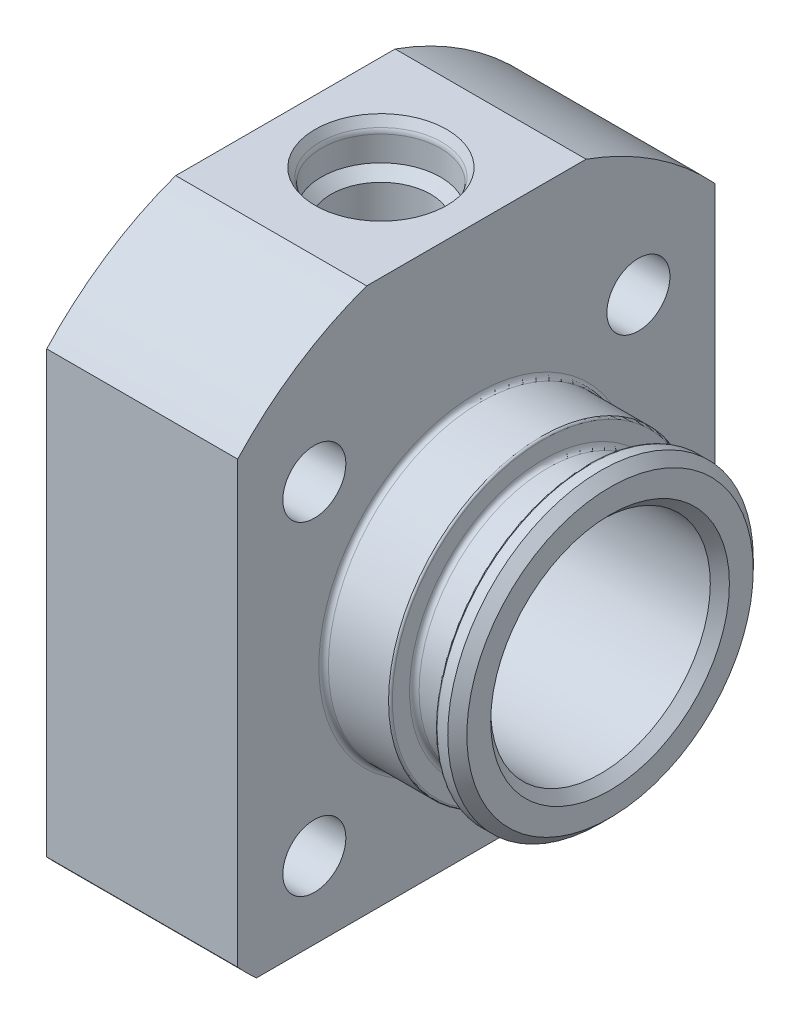
SolidWorks part; units mm, degrees
material "Сплав 3М ОСТ 1.92077-91"
ref_plane "Plane1" through (0, 0, 0) normal (0, 0, 1) x (1, 0, 0)
ref_plane "Plane2" through (0, 0, 0) normal (0, 1, 0) x (1, 0, 0)
ref_plane "Plane3" through (0, 0, 0) normal (1, 0, 0) x (0, 0, -1)
sketch "Эскиз1" plane through (0, 0, 0) normal (0, 0, 1) x (1, 0, 0)
  line L0 (0, 0) -> (-37.8297, 0) construction
  line L1 (20, 34) -> (20, 16)
  line L2 (-10, 0) -> (4, 0)
  line L3 (0, 11) -> (0, 34)
  line L4 (0, 34) -> (20, 34)
  line L5 (34, 11.5) -> (34, 16)
  line L6 (20, 16) -> (27, 16)
  line L7 (0, 11) -> (-9.5981, 11)
  line L8 (-10, 9.5) -> (-10, 0)
  line L9 (31.7, 16) -> (31.7, 13.5)
  line L10 (31.7, 13.5) -> (27, 13.5)
  line L11 (27, 13.5) -> (27, 16)
  line L12 (31.7, 16) -> (34, 16)
  line L13 (-9.5981, 11) -> (-10, 9.5)
  line L14 (34, 11.5) -> (4, 11.5)
  line L15 (4, 11.5) -> (4, 0)
  dimension "D1" = 68
  dimension "D2" = 34
  dimension "D3" = 32
  dimension "D4" = 14
  dimension "D5" = 22
  dimension "D6" = 10
  dimension "D7" = 4.7
  dimension "D8" = 2.5
  dimension "D9" = 7
  dimension "D10" = 19
  dimension "D11" = 15
  dimension "D12" = 23
  dimension "D13" = 14
revolve "Повернуть1" add sketch "Эскиз1" angle 360 about L0
sketch "Эскиз2" plane through (0, 0, 0) normal (-1, 0, 0) x (0, 0, 1)
  line L0 (-11.4891, 32) -> (11.4891, 32)
  line L1 (-25, 23.0434) -> (-25, -25)
  line L2 (-25, -25) -> (25, -25)
  line L3 (25, -25) -> (25, 23.0434)
  line L4 (0, 0) -> (0, -25) construction
  circle A0 centre (0, 0) radius 34 construction
  arc A1 (-11.4891, 32) -> (-25, 23.0434) centre (0, 0) ccw
  arc A2 (25, 23.0434) -> (11.4891, 32) centre (0, 0) ccw
  point P0 (0, 0)
  dimension "D1" = 25
  dimension "D2" = 50
  dimension "D3" = 57
extrude "Вырез-Вытянуть1" cut sketch "Эскиз2" against normal through all flip side to cut
sketch "Sketch4" plane through (-10, -1.1882, -2.3798) normal (-1, 0, 0) x (0, 0, 1)
  line L0 (2.3798, 1.1882) -> (2.3798, 3.2982) construction
  line L1 (2.3798, 1.1882) -> (7.4898, 1.1882) construction
  point P0 (2.3798, 1.1882)
  point P3 (7.4898, 1.1882)
  dimension "D1" = 5.11
  dimension "D2" = 2.11
  dimension "D3" = 90
ref_plane "Plane4_для_эскиза_отверстия" through (-10, 0, 0) normal (0, 1, 0) x (-1, 0, 0)
ref_plane "Plane5_начало_резьбы" through (-10, 0, 0) normal (1, 0, 0) x (0, -1, 0)
sketch "Sketch2" plane through (-10, 0, 0) normal (0, 1, 0) x (0, 0, -1)
  line L0 (0, 0) -> (0, -63.1034)
  line L1 (-6.9, 0) -> (-6.384, -0.8938)
  line L2 (6.384, -0.8938) -> (6.9, 0) construction
  line L3 (-6.25, -1.3938) -> (-6.25, -4)
  line L4 (-6.25, -4) -> (-5.215, -5.035)
  line L5 (-5.215, -5.035) -> (-5.215, -13)
  line L6 (-5.165, -60) -> (0, -63.1034)
  line L7 (-6.9, 0) -> (0, 0)
  line L8 (0, 0) -> (0, 3.9197) construction
  line L9 (-5.215, -13) -> (-5.165, -13)
  line L11 (6.25, -1.3938) -> (6.25, -4) construction
  line L12 (-5.165, -13) -> (-5.165, -60)
  line L13 (6.25, -4) -> (5.215, -5.035) construction
  line L14 (0, -63.1034) -> (5.165, -60) construction
  arc A0 (-6.384, -0.8938) -> (-6.25, -1.3938) centre (-7.25, -1.3938) cw
  arc A1 (6.25, -1.3938) -> (6.384, -0.8938) centre (7.25, -1.3938) cw construction
  point P2 (-6, -13)
  point P19 (-6.9, 0)
  dimension "D9" = 1
  dimension "D10" = 1
  dimension "D1_уплотнение" = 12.5
  dimension "D2_фаска" = 13.8
  dimension "D3_под_резьбу" = 10.43
  dimension "D4_глубина_сверления" = 60
  dimension "D5" = 4
  dimension "D6" = 60
  dimension "D7" = 90
  dimension "D8" = 118
  dimension "D11" = 0.05
  dimension "D1_диаметр" = 12
  dimension "D2_глубина_резьбы" = 13
revolve "Cut-Revolve1" cut sketch "Sketch2" angle 360 about L8
cosmetic thread "Условное изображение резьбы1" parameters "D1_диаметр"=12
other "Отв_ГОСТ_19529-74 - <1>"
hole_wizard "Цековка для винта с внутренним шестигранником M61" positions "Эскиз6" profile "Эскиз5" counterbore size "M6" standard "ISO" end condition through all
sketch "Эскиз6" plane through (0, 0, 0) normal (-1, 0, 0) x (0, 0, 1)
  line L0 (16.9706, 16.9706) -> (0, 0) construction
  line L1 (0, 0) -> (0, 18.0622) construction
  point P0 (16.9706, 16.9706)
  dimension "D1" = 45
  dimension "D2" = 24
sketch "Эскиз5" plane through (0, 16.9706, 16.9706) normal (0, 1, 0) x (0, 0, 1)
  line L0 (0, 0) -> (0, 34)
  line L1 (0, 34) -> (3.3, 34)
  line L3 (3.3, 34) -> (3.3, 6.4)
  line L4 (3.3, 6.4) -> (5.5, 6.4)
  line L5 (5.5, 6.4) -> (5.5, 0)
  line L7 (5.5, 0) -> (0, 0)
  line L11 (0, -6.35) -> (0, 107.95) construction
  dimension "Диаметр сквозного отверстия" = 6.6
  dimension "Глубина сквозного отверстия" = 34
  dimension "Диаметр цековки" = 11
  dimension "Глубина цековки" = 6.4
pattern_circular "Круговой массив1" count 4 over 360 about axis through (0, 0, 0) along (1, 0, 0) of "Цековка для винта с внутренним шестигранником M61"
sketch "Sketch42" plane through (11.865, 32, 1.0142) normal (0, 1, 0) x (-1, 0, 0)
  line L0 (1.865, -1.0142) -> (1.865, 1.0958) construction
  line L1 (1.865, -1.0142) -> (6.975, -1.0142) construction
  line L2 (11.865, 10.4749) -> (11.865, -12.5033) construction
  point P0 (1.865, -1.0142)
  point P3 (6.975, -1.0142)
  dimension "D1" = 5.11
  dimension "D2" = 2.11
  dimension "D3" = 90
  dimension "D4" = 10
ref_plane "Plane4_для_эскиза_отверстия2" through (10, 32, 0) normal (0, 0, 1) x (1, 0, 0)
ref_plane "Plane5_начало_резьбы2" through (0, 32, 0) normal (0, -1, 0) x (-1, 0, 0)
sketch "Sketch22" plane through (10, 32, 0) normal (0, 0, 1) x (1, 0, 0)
  line L0 (0, 0) -> (0, -35.1034)
  line L1 (-6.9, 0) -> (-6.384, -0.8938)
  line L2 (6.384, -0.8938) -> (6.9, 0) construction
  line L3 (-6.25, -1.3938) -> (-6.25, -4)
  line L4 (-6.25, -4) -> (-5.215, -5.035)
  line L5 (-5.215, -5.035) -> (-5.215, -13)
  line L6 (-5.165, -32) -> (0, -35.1034)
  line L7 (-6.9, 0) -> (0, 0)
  line L8 (0, 0) -> (0, 3.9197) construction
  line L9 (-5.215, -13) -> (-5.165, -13)
  line L11 (6.25, -1.3938) -> (6.25, -4) construction
  line L12 (-5.165, -13) -> (-5.165, -32)
  line L13 (6.25, -4) -> (5.215, -5.035) construction
  line L14 (0, -35.1034) -> (5.165, -32) construction
  arc A0 (-6.384, -0.8938) -> (-6.25, -1.3938) centre (-7.25, -1.3938) cw
  arc A1 (6.25, -1.3938) -> (6.384, -0.8938) centre (7.25, -1.3938) cw construction
  point P2 (-6, -13)
  point P19 (-6.9, 0)
  dimension "D9" = 1
  dimension "D10" = 1
  dimension "D1_уплотнение" = 12.5
  dimension "D2_фаска" = 13.8
  dimension "D3_под_резьбу" = 10.43
  dimension "D4_глубина_сверления" = 32
  dimension "D5" = 4
  dimension "D6" = 60
  dimension "D7" = 90
  dimension "D8" = 118
  dimension "D11" = 0.05
  dimension "D1_диаметр" = 12
  dimension "D2_глубина_резьбы" = 13
revolve "Cut-Revolve12" cut sketch "Sketch22" angle 360 about L8
cosmetic thread "Условное изображение резьбы3" parameters "D1_диаметр"=12
other "Отв_ГОСТ_19529-74 - <2>"
sketch "Эскиз11" plane through (-10, 0, 0) normal (-1, 0, 0) x (0, 0, 1)
  line L1 (0, 10.9697) -> (-9.5, 5.4848)
  line L2 (-9.5, 5.4848) -> (-9.5, -5.4848)
  line L3 (-9.5, -5.4848) -> (0, -10.9697)
  line L4 (0, -10.9697) -> (9.5, -5.4848)
  line L5 (9.5, -5.4848) -> (9.5, 5.4848)
  line L6 (9.5, 5.4848) -> (0, 10.9697)
  circle A0 centre (0, 0) radius 9.5 construction
  dimension "D1" = 19
extrude "Вырез-Вытянуть2" cut sketch "Эскиз11" against normal blind 9 flip side to cut
chamfer "Фаска1" distance 1 angle 45 2 edges at (34, 0, -11.5) (34, 0, -16)
fillet "Скругление1" radius 0.2 2 edges at (31.7, 0, -16) (27, 0, -16)
fillet "Скругление2" radius 0.5 2 edges at (31.7, 0, -13.5) (27, 0, -13.5)
fillet "Скругление3" radius 0.5 2 edges at (4, 0, -11.5) (20, 0, -16)
